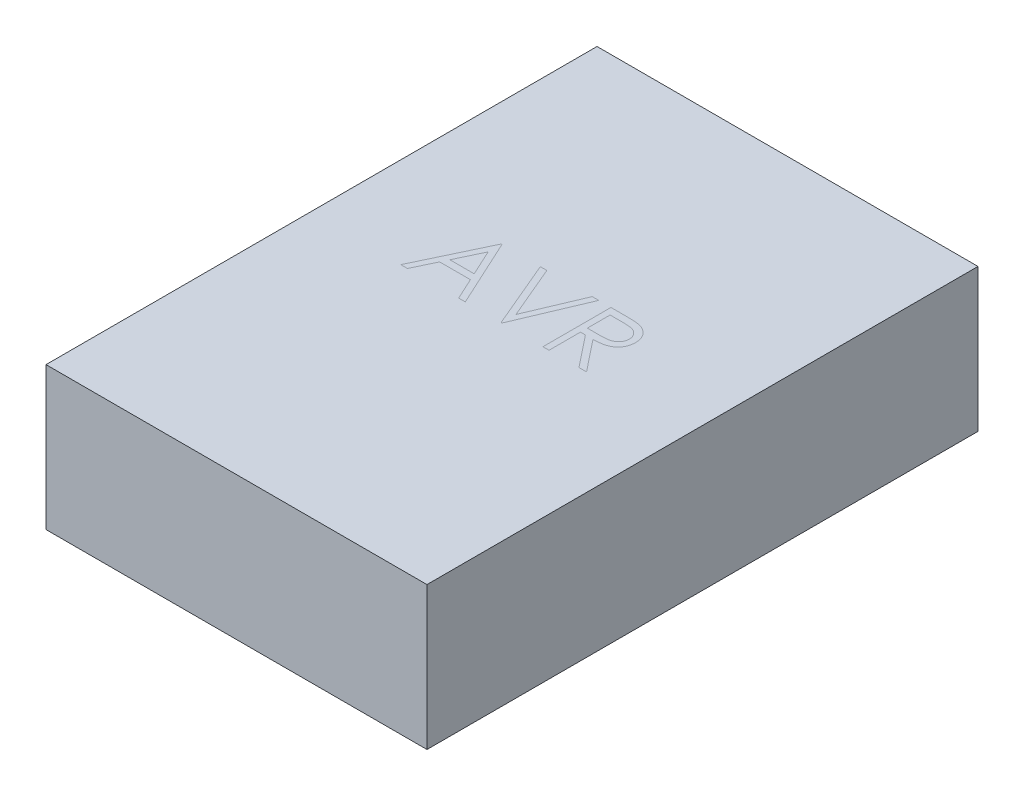
SolidWorks part; units mm, degrees
ref_plane "Front Plane" through (0, 0, 0) normal (0, 0, 1) x (1, 0, 0)
ref_plane "Top Plane" through (0, 0, 0) normal (0, 1, 0) x (1, 0, 0)
ref_plane "Right Plane" through (0, 0, 0) normal (1, 0, 0) x (0, 0, -1)
sketch "Sketch1" plane through (0, 0, 0) normal (0, 1, 0) x (1, 0, 0)
  line L1 (-140, 202.5) -> (140, 202.5)
  line L2 (-140, 202.5) -> (-140, -202.5)
  line L3 (-140, -202.5) -> (140, -202.5)
  line L4 (140, 202.5) -> (140, -202.5)
  line L5 (-140, 202.5) -> (140, -202.5) construction
  line L6 (-140, -202.5) -> (140, 202.5) construction
  point P0 (0, 0)
  dimension "D1" = 280
  dimension "D2" = 405
extrude "Boss-Extrude1" add sketch "Sketch1" along normal blind 105
sketch "Sketch2" plane through (0, 105, 0) normal (0, 1, 0) x (1, 0, 0)
  text T0 "AVR" font "Century Gothic" height 50
split line "Split Line1"
